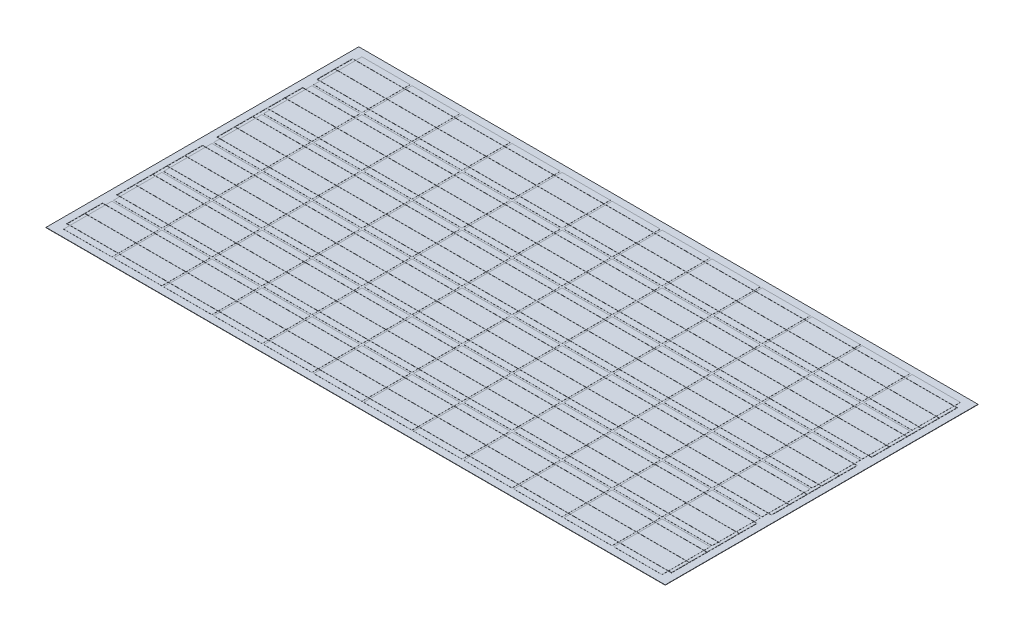
SolidWorks part; units mm, degrees
ref_plane "Front Plane" through (0, 0, 0) normal (0, 0, 1) x (1, 0, 0)
ref_plane "Top Plane" through (0, 0, 0) normal (0, 1, 0) x (1, 0, 0)
ref_plane "Right Plane" through (0, 0, 0) normal (1, 0, 0) x (0, 0, -1)
sketch "Sketch1" plane through (0, 0, 0) normal (0, 1, 0) x (1, 0, 0)
  line L0 (81.8, 76.2) -> (81.8, -76.2)
  line L1 (-76.2, 76.2) -> (76.2, 76.2)
  line L2 (-76.2, 76.2) -> (-76.2, -76.2)
  line L3 (-76.2, -76.2) -> (76.2, -76.2)
  line L4 (76.2, 76.2) -> (76.2, -76.2)
  line L5 (-76.2, 76.2) -> (76.2, -76.2) construction
  line L6 (-76.2, -76.2) -> (76.2, 76.2) construction
  line L7 (81.8, 76.2) -> (234.2, 76.2)
  line L8 (234.2, 76.2) -> (234.2, -76.2)
  line L9 (81.8, -76.2) -> (234.2, -76.2)
  line L10 (239.8, 76.2) -> (239.8, -76.2)
  line L11 (239.8, 76.2) -> (392.2, 76.2)
  line L12 (392.2, 76.2) -> (392.2, -76.2)
  line L13 (239.8, -76.2) -> (392.2, -76.2)
  line L14 (397.8, 76.2) -> (397.8, -76.2)
  line L15 (397.8, 76.2) -> (550.2, 76.2)
  line L16 (550.2, 76.2) -> (550.2, -76.2)
  line L17 (397.8, -76.2) -> (550.2, -76.2)
  line L18 (555.8, 76.2) -> (555.8, -76.2)
  line L19 (555.8, 76.2) -> (708.2, 76.2)
  line L20 (708.2, 76.2) -> (708.2, -76.2)
  line L21 (555.8, -76.2) -> (708.2, -76.2)
  line L22 (713.8, 76.2) -> (713.8, -76.2)
  line L23 (713.8, 76.2) -> (866.2, 76.2)
  line L24 (866.2, 76.2) -> (866.2, -76.2)
  line L25 (713.8, -76.2) -> (866.2, -76.2)
  line L26 (871.8, 76.2) -> (871.8, -76.2)
  line L27 (871.8, 76.2) -> (1024.2, 76.2)
  line L28 (1024.2, 76.2) -> (1024.2, -76.2)
  line L29 (871.8, -76.2) -> (1024.2, -76.2)
  line L30 (1029.8, 76.2) -> (1029.8, -76.2)
  line L31 (1029.8, 76.2) -> (1182.2, 76.2)
  line L32 (1182.2, 76.2) -> (1182.2, -76.2)
  line L33 (1029.8, -76.2) -> (1182.2, -76.2)
  line L34 (1187.8, 76.2) -> (1187.8, -76.2)
  line L35 (1187.8, 76.2) -> (1340.2, 76.2)
  line L36 (1340.2, 76.2) -> (1340.2, -76.2)
  line L37 (1187.8, -76.2) -> (1340.2, -76.2)
  line L38 (1345.8, 76.2) -> (1345.8, -76.2)
  line L39 (1345.8, 76.2) -> (1498.2, 76.2)
  line L40 (1498.2, 76.2) -> (1498.2, -76.2)
  line L41 (1345.8, -76.2) -> (1498.2, -76.2)
  line L42 (1503.8, 76.2) -> (1503.8, -76.2)
  line L43 (1503.8, 76.2) -> (1656.2, 76.2)
  line L44 (1656.2, 76.2) -> (1656.2, -76.2)
  line L45 (1503.8, -76.2) -> (1656.2, -76.2)
  line L46 (1661.8, 76.2) -> (1661.8, -76.2)
  line L47 (1661.8, 76.2) -> (1814.2, 76.2)
  line L48 (1814.2, 76.2) -> (1814.2, -76.2)
  line L49 (1661.8, -76.2) -> (1814.2, -76.2)
  line L50 (81.8, 234.2) -> (81.8, 81.8)
  line L51 (81.8, 234.2) -> (234.2, 234.2)
  line L52 (234.2, 234.2) -> (234.2, 81.8)
  line L53 (81.8, 81.8) -> (234.2, 81.8)
  line L54 (239.8, 234.2) -> (239.8, 81.8)
  line L55 (239.8, 234.2) -> (392.2, 234.2)
  line L56 (392.2, 234.2) -> (392.2, 81.8)
  line L57 (239.8, 81.8) -> (392.2, 81.8)
  line L58 (397.8, 234.2) -> (397.8, 81.8)
  line L59 (397.8, 234.2) -> (550.2, 234.2)
  line L60 (550.2, 234.2) -> (550.2, 81.8)
  line L61 (397.8, 81.8) -> (550.2, 81.8)
  line L62 (555.8, 234.2) -> (555.8, 81.8)
  line L63 (555.8, 234.2) -> (708.2, 234.2)
  line L64 (708.2, 234.2) -> (708.2, 81.8)
  line L65 (555.8, 81.8) -> (708.2, 81.8)
  line L66 (713.8, 234.2) -> (713.8, 81.8)
  line L67 (713.8, 234.2) -> (866.2, 234.2)
  line L68 (866.2, 234.2) -> (866.2, 81.8)
  line L69 (713.8, 81.8) -> (866.2, 81.8)
  line L70 (871.8, 234.2) -> (871.8, 81.8)
  line L71 (871.8, 234.2) -> (1024.2, 234.2)
  line L72 (1024.2, 234.2) -> (1024.2, 81.8)
  line L73 (871.8, 81.8) -> (1024.2, 81.8)
  line L74 (1029.8, 234.2) -> (1029.8, 81.8)
  line L75 (1029.8, 234.2) -> (1182.2, 234.2)
  line L76 (1182.2, 234.2) -> (1182.2, 81.8)
  line L77 (1029.8, 81.8) -> (1182.2, 81.8)
  line L78 (1187.8, 234.2) -> (1187.8, 81.8)
  line L79 (1187.8, 234.2) -> (1340.2, 234.2)
  line L80 (1340.2, 234.2) -> (1340.2, 81.8)
  line L81 (1187.8, 81.8) -> (1340.2, 81.8)
  line L82 (1345.8, 234.2) -> (1345.8, 81.8)
  line L83 (1345.8, 234.2) -> (1498.2, 234.2)
  line L84 (1498.2, 234.2) -> (1498.2, 81.8)
  line L85 (1345.8, 81.8) -> (1498.2, 81.8)
  line L86 (1503.8, 234.2) -> (1503.8, 81.8)
  line L87 (1503.8, 234.2) -> (1656.2, 234.2)
  line L88 (1656.2, 234.2) -> (1656.2, 81.8)
  line L89 (1503.8, 81.8) -> (1656.2, 81.8)
  line L90 (1661.8, 234.2) -> (1661.8, 81.8)
  line L91 (1661.8, 234.2) -> (1814.2, 234.2)
  line L92 (1814.2, 234.2) -> (1814.2, 81.8)
  line L93 (1661.8, 81.8) -> (1814.2, 81.8)
  line L94 (81.8, 392.2) -> (81.8, 239.8)
  line L95 (81.8, 392.2) -> (234.2, 392.2)
  line L96 (234.2, 392.2) -> (234.2, 239.8)
  line L97 (81.8, 239.8) -> (234.2, 239.8)
  line L98 (239.8, 392.2) -> (239.8, 239.8)
  line L99 (239.8, 392.2) -> (392.2, 392.2)
  line L100 (392.2, 392.2) -> (392.2, 239.8)
  line L101 (239.8, 239.8) -> (392.2, 239.8)
  line L102 (397.8, 392.2) -> (397.8, 239.8)
  line L103 (397.8, 392.2) -> (550.2, 392.2)
  line L104 (550.2, 392.2) -> (550.2, 239.8)
  line L105 (397.8, 239.8) -> (550.2, 239.8)
  line L106 (555.8, 392.2) -> (555.8, 239.8)
  line L107 (555.8, 392.2) -> (708.2, 392.2)
  line L108 (708.2, 392.2) -> (708.2, 239.8)
  line L109 (555.8, 239.8) -> (708.2, 239.8)
  line L110 (713.8, 392.2) -> (713.8, 239.8)
  line L111 (713.8, 392.2) -> (866.2, 392.2)
  line L112 (866.2, 392.2) -> (866.2, 239.8)
  line L113 (713.8, 239.8) -> (866.2, 239.8)
  line L114 (871.8, 392.2) -> (871.8, 239.8)
  line L115 (871.8, 392.2) -> (1024.2, 392.2)
  line L116 (1024.2, 392.2) -> (1024.2, 239.8)
  line L117 (871.8, 239.8) -> (1024.2, 239.8)
  line L118 (1029.8, 392.2) -> (1029.8, 239.8)
  line L119 (1029.8, 392.2) -> (1182.2, 392.2)
  line L120 (1182.2, 392.2) -> (1182.2, 239.8)
  line L121 (1029.8, 239.8) -> (1182.2, 239.8)
  line L122 (1187.8, 392.2) -> (1187.8, 239.8)
  line L123 (1187.8, 392.2) -> (1340.2, 392.2)
  line L124 (1340.2, 392.2) -> (1340.2, 239.8)
  line L125 (1187.8, 239.8) -> (1340.2, 239.8)
  line L126 (1345.8, 392.2) -> (1345.8, 239.8)
  line L127 (1345.8, 392.2) -> (1498.2, 392.2)
  line L128 (1498.2, 392.2) -> (1498.2, 239.8)
  line L129 (1345.8, 239.8) -> (1498.2, 239.8)
  line L130 (1503.8, 392.2) -> (1503.8, 239.8)
  line L131 (1503.8, 392.2) -> (1656.2, 392.2)
  line L132 (1656.2, 392.2) -> (1656.2, 239.8)
  line L133 (1503.8, 239.8) -> (1656.2, 239.8)
  line L134 (1661.8, 392.2) -> (1661.8, 239.8)
  line L135 (1661.8, 392.2) -> (1814.2, 392.2)
  line L136 (1814.2, 392.2) -> (1814.2, 239.8)
  line L137 (1661.8, 239.8) -> (1814.2, 239.8)
  line L138 (81.8, 550.2) -> (81.8, 397.8)
  line L139 (81.8, 550.2) -> (234.2, 550.2)
  line L140 (234.2, 550.2) -> (234.2, 397.8)
  line L141 (81.8, 397.8) -> (234.2, 397.8)
  line L142 (239.8, 550.2) -> (239.8, 397.8)
  line L143 (239.8, 550.2) -> (392.2, 550.2)
  line L144 (392.2, 550.2) -> (392.2, 397.8)
  line L145 (239.8, 397.8) -> (392.2, 397.8)
  line L146 (397.8, 550.2) -> (397.8, 397.8)
  line L147 (397.8, 550.2) -> (550.2, 550.2)
  line L148 (550.2, 550.2) -> (550.2, 397.8)
  line L149 (397.8, 397.8) -> (550.2, 397.8)
  line L150 (555.8, 550.2) -> (555.8, 397.8)
  line L151 (555.8, 550.2) -> (708.2, 550.2)
  line L152 (708.2, 550.2) -> (708.2, 397.8)
  line L153 (555.8, 397.8) -> (708.2, 397.8)
  line L154 (713.8, 550.2) -> (713.8, 397.8)
  line L155 (713.8, 550.2) -> (866.2, 550.2)
  line L156 (866.2, 550.2) -> (866.2, 397.8)
  line L157 (713.8, 397.8) -> (866.2, 397.8)
  line L158 (871.8, 550.2) -> (871.8, 397.8)
  line L159 (871.8, 550.2) -> (1024.2, 550.2)
  line L160 (1024.2, 550.2) -> (1024.2, 397.8)
  line L161 (871.8, 397.8) -> (1024.2, 397.8)
  line L162 (1029.8, 550.2) -> (1029.8, 397.8)
  line L163 (1029.8, 550.2) -> (1182.2, 550.2)
  line L164 (1182.2, 550.2) -> (1182.2, 397.8)
  line L165 (1029.8, 397.8) -> (1182.2, 397.8)
  line L166 (1187.8, 550.2) -> (1187.8, 397.8)
  line L167 (1187.8, 550.2) -> (1340.2, 550.2)
  line L168 (1340.2, 550.2) -> (1340.2, 397.8)
  line L169 (1187.8, 397.8) -> (1340.2, 397.8)
  line L170 (1345.8, 550.2) -> (1345.8, 397.8)
  line L171 (1345.8, 550.2) -> (1498.2, 550.2)
  line L172 (1498.2, 550.2) -> (1498.2, 397.8)
  line L173 (1345.8, 397.8) -> (1498.2, 397.8)
  line L174 (1503.8, 550.2) -> (1503.8, 397.8)
  line L175 (1503.8, 550.2) -> (1656.2, 550.2)
  line L176 (1656.2, 550.2) -> (1656.2, 397.8)
  line L177 (1503.8, 397.8) -> (1656.2, 397.8)
  line L178 (1661.8, 550.2) -> (1661.8, 397.8)
  line L179 (1661.8, 550.2) -> (1814.2, 550.2)
  line L180 (1814.2, 550.2) -> (1814.2, 397.8)
  line L181 (1661.8, 397.8) -> (1814.2, 397.8)
  line L182 (81.8, 708.2) -> (81.8, 555.8)
  line L183 (81.8, 708.2) -> (234.2, 708.2)
  line L184 (234.2, 708.2) -> (234.2, 555.8)
  line L185 (81.8, 555.8) -> (234.2, 555.8)
  line L186 (239.8, 708.2) -> (239.8, 555.8)
  line L187 (239.8, 708.2) -> (392.2, 708.2)
  line L188 (392.2, 708.2) -> (392.2, 555.8)
  line L189 (239.8, 555.8) -> (392.2, 555.8)
  line L190 (397.8, 708.2) -> (397.8, 555.8)
  line L191 (397.8, 708.2) -> (550.2, 708.2)
  line L192 (550.2, 708.2) -> (550.2, 555.8)
  line L193 (397.8, 555.8) -> (550.2, 555.8)
  line L194 (555.8, 708.2) -> (555.8, 555.8)
  line L195 (555.8, 708.2) -> (708.2, 708.2)
  line L196 (708.2, 708.2) -> (708.2, 555.8)
  line L197 (555.8, 555.8) -> (708.2, 555.8)
  line L198 (713.8, 708.2) -> (713.8, 555.8)
  line L199 (713.8, 708.2) -> (866.2, 708.2)
  line L200 (866.2, 708.2) -> (866.2, 555.8)
  line L201 (713.8, 555.8) -> (866.2, 555.8)
  line L202 (871.8, 708.2) -> (871.8, 555.8)
  line L203 (871.8, 708.2) -> (1024.2, 708.2)
  line L204 (1024.2, 708.2) -> (1024.2, 555.8)
  line L205 (871.8, 555.8) -> (1024.2, 555.8)
  line L206 (1029.8, 708.2) -> (1029.8, 555.8)
  line L207 (1029.8, 708.2) -> (1182.2, 708.2)
  line L208 (1182.2, 708.2) -> (1182.2, 555.8)
  line L209 (1029.8, 555.8) -> (1182.2, 555.8)
  line L210 (1187.8, 708.2) -> (1187.8, 555.8)
  line L211 (1187.8, 708.2) -> (1340.2, 708.2)
  line L212 (1340.2, 708.2) -> (1340.2, 555.8)
  line L213 (1187.8, 555.8) -> (1340.2, 555.8)
  line L214 (1345.8, 708.2) -> (1345.8, 555.8)
  line L215 (1345.8, 708.2) -> (1498.2, 708.2)
  line L216 (1498.2, 708.2) -> (1498.2, 555.8)
  line L217 (1345.8, 555.8) -> (1498.2, 555.8)
  line L218 (1503.8, 708.2) -> (1503.8, 555.8)
  line L219 (1503.8, 708.2) -> (1656.2, 708.2)
  line L220 (1656.2, 708.2) -> (1656.2, 555.8)
  line L221 (1503.8, 555.8) -> (1656.2, 555.8)
  line L222 (1661.8, 708.2) -> (1661.8, 555.8)
  line L223 (1661.8, 708.2) -> (1814.2, 708.2)
  line L224 (1814.2, 708.2) -> (1814.2, 555.8)
  line L225 (1661.8, 555.8) -> (1814.2, 555.8)
  line L226 (81.8, 866.2) -> (81.8, 713.8)
  line L227 (81.8, 866.2) -> (234.2, 866.2)
  line L228 (234.2, 866.2) -> (234.2, 713.8)
  line L229 (81.8, 713.8) -> (234.2, 713.8)
  line L230 (239.8, 866.2) -> (239.8, 713.8)
  line L231 (239.8, 866.2) -> (392.2, 866.2)
  line L232 (392.2, 866.2) -> (392.2, 713.8)
  line L233 (239.8, 713.8) -> (392.2, 713.8)
  line L234 (397.8, 866.2) -> (397.8, 713.8)
  line L235 (397.8, 866.2) -> (550.2, 866.2)
  line L236 (550.2, 866.2) -> (550.2, 713.8)
  line L237 (397.8, 713.8) -> (550.2, 713.8)
  line L238 (555.8, 866.2) -> (555.8, 713.8)
  line L239 (555.8, 866.2) -> (708.2, 866.2)
  line L240 (708.2, 866.2) -> (708.2, 713.8)
  line L241 (555.8, 713.8) -> (708.2, 713.8)
  line L242 (713.8, 866.2) -> (713.8, 713.8)
  line L243 (713.8, 866.2) -> (866.2, 866.2)
  line L244 (866.2, 866.2) -> (866.2, 713.8)
  line L245 (713.8, 713.8) -> (866.2, 713.8)
  line L246 (871.8, 866.2) -> (871.8, 713.8)
  line L247 (871.8, 866.2) -> (1024.2, 866.2)
  line L248 (1024.2, 866.2) -> (1024.2, 713.8)
  line L249 (871.8, 713.8) -> (1024.2, 713.8)
  line L250 (1029.8, 866.2) -> (1029.8, 713.8)
  line L251 (1029.8, 866.2) -> (1182.2, 866.2)
  line L252 (1182.2, 866.2) -> (1182.2, 713.8)
  line L253 (1029.8, 713.8) -> (1182.2, 713.8)
  line L254 (1187.8, 866.2) -> (1187.8, 713.8)
  line L255 (1187.8, 866.2) -> (1340.2, 866.2)
  line L256 (1340.2, 866.2) -> (1340.2, 713.8)
  line L257 (1187.8, 713.8) -> (1340.2, 713.8)
  line L258 (1345.8, 866.2) -> (1345.8, 713.8)
  line L259 (1345.8, 866.2) -> (1498.2, 866.2)
  line L260 (1498.2, 866.2) -> (1498.2, 713.8)
  line L261 (1345.8, 713.8) -> (1498.2, 713.8)
  line L262 (1503.8, 866.2) -> (1503.8, 713.8)
  line L263 (1503.8, 866.2) -> (1656.2, 866.2)
  line L264 (1656.2, 866.2) -> (1656.2, 713.8)
  line L265 (1503.8, 713.8) -> (1656.2, 713.8)
  line L266 (1661.8, 866.2) -> (1661.8, 713.8)
  line L267 (1661.8, 866.2) -> (1814.2, 866.2)
  line L268 (1814.2, 866.2) -> (1814.2, 713.8)
  line L269 (1661.8, 713.8) -> (1814.2, 713.8)
  line L270 (-76.2, 234.2) -> (-76.2, 81.8)
  line L271 (-76.2, 234.2) -> (76.2, 234.2)
  line L272 (76.2, 234.2) -> (76.2, 81.8)
  line L273 (-76.2, 81.8) -> (76.2, 81.8)
  line L274 (-76.2, 392.2) -> (-76.2, 239.8)
  line L275 (-76.2, 392.2) -> (76.2, 392.2)
  line L276 (76.2, 392.2) -> (76.2, 239.8)
  line L277 (-76.2, 239.8) -> (76.2, 239.8)
  line L278 (-76.2, 550.2) -> (-76.2, 397.8)
  line L279 (-76.2, 550.2) -> (76.2, 550.2)
  line L280 (76.2, 550.2) -> (76.2, 397.8)
  line L281 (-76.2, 397.8) -> (76.2, 397.8)
  line L282 (-76.2, 708.2) -> (-76.2, 555.8)
  line L283 (-76.2, 708.2) -> (76.2, 708.2)
  line L284 (76.2, 708.2) -> (76.2, 555.8)
  line L285 (-76.2, 555.8) -> (76.2, 555.8)
  line L286 (-76.2, 866.2) -> (-76.2, 713.8)
  line L287 (-76.2, 866.2) -> (76.2, 866.2)
  line L288 (76.2, 866.2) -> (76.2, 713.8)
  line L289 (-76.2, 713.8) -> (76.2, 713.8)
  line L290 (-76.2, 76.2) -> (81.8, 76.2) construction
  line L291 (-76.2, 76.2) -> (-76.2, 234.2) construction
  point P0 (0, 0)
  dimension "D1" = 152.4
  dimension "D2" = 152.4
  dimension "D5" = 158
  dimension "D6" = 158
  dimension "D3" = 12
  dimension "D4" = 6
extrude "Boss-Extrude1" add sketch "Sketch1" along normal blind 0.3
sketch "Sketch2" plane through (0, 0, 0) normal (0, -1, 0) x (1, 0, 0)
  line L1 (1846.9962, -889) -> (-109.0038, -889)
  line L2 (1846.9962, -889) -> (1846.9962, 99)
  line L3 (1846.9962, 99) -> (-109.0038, 99)
  line L4 (-109.0038, -889) -> (-109.0038, 99)
  line L5 (1846.9962, -889) -> (-109.0038, 99) construction
  line L6 (1846.9962, 99) -> (-109.0038, -889) construction
  line L9 (866.2, -397.8) -> (866.2, -550.2) construction
  line L10 (1024.2, -392.2) -> (871.8, -392.2) construction
  point P0 (868.9962, -395)
  point P5 (0, 0)
  point P6 (868.9618, -395.0845)
  point P7 (868.8142, -395.0837)
  point P8 (0, 0)
  point P10 (0, 0)
  point P11 (868.9962, -394.7196)
  dimension "D1" = 1956
  dimension "D2" = 988
  dimension "D3" = 2.7962
  dimension "D4" = 2.8
extrude "Boss-Extrude2" add sketch "Sketch2" along normal blind 1
sketch "Sketch5" plane through (0, -1, 0) normal (0, -1, 0) x (1, 0, 0)
  line L0 (-109.0038, 99) -> (-109.0038, -889) construction
  line L1 (125.9962, -305) -> (40.9962, -305)
  line L2 (125.9962, -305) -> (125.9962, -485)
  line L3 (125.9962, -485) -> (40.9962, -485)
  line L4 (40.9962, -305) -> (40.9962, -485)
  line L5 (125.9962, -305) -> (40.9962, -485) construction
  line L6 (125.9962, -485) -> (40.9962, -305) construction
  point P0 (83.4962, -395)
  point P7 (40.9962, -395)
  point P8 (-109.0038, -395)
  dimension "D1" = 180
  dimension "D2" = 85
  dimension "D3" = 150
extrude "Boss-Extrude3" add sketch "Sketch5" along normal blind 20
sketch "Sketch3" plane through (0, 0.3, 0) normal (0, 1, 0) x (1, 0, 0)
  line L0 (1824.2, 846.2) -> (1824.2, 575.8)
  line L1 (1824.2, 530.2) -> (1824.2, 259.8)
  line L2 (1824.2, -56.2) -> (1824.2, 214.2)
  line L3 (1814.2, 81.8) -> (1814.2, 234.2) construction
  line L4 (1814.2, 866.2) -> (1661.8, 866.2) construction
  line L5 (-86.2, 417.8) -> (-86.2, 688.2)
  line L6 (-86.2, 372.2) -> (-86.2, 101.8)
  line L7 (-86.2, 846.2) -> (-86.2, 733.8)
  line L8 (-86.2, -56.2) -> (-86.2, 56.2)
  line L9 (-76.2, 866.2) -> (-76.2, 713.8) construction
  line L11 (-86.2, 846.2) -> (1824.2, 846.2)
  line L12 (-86.2, 733.8) -> (1824.2, 733.8)
  line L13 (-86.2, 790) -> (1824.2, 790)
  line L14 (1824.2, 688.2) -> (-86.2, 688.2)
  line L15 (-86.2, 575.8) -> (1824.2, 575.8)
  line L16 (-86.2, 530.2) -> (1824.2, 530.2)
  line L17 (-86.2, 259.8) -> (1824.2, 259.8)
  line L18 (-86.2, 214.2) -> (1824.2, 214.2)
  line L19 (1824.2, 101.8) -> (-86.2, 101.8)
  line L20 (1824.2, 56.2) -> (-86.2, 56.2)
  line L21 (1824.2, -56.2) -> (-86.2, -56.2)
  line L22 (-86.2, 0) -> (1824.2, 0)
  line L23 (1824.2, 372.2) -> (-86.2, 372.2)
  line L24 (1824.2, 417.8) -> (-86.2, 417.8)
  line L25 (-86.2, 632) -> (1824.2, 632)
  line L26 (-86.2, 474) -> (1824.2, 474)
  line L27 (-86.2, 316) -> (1824.2, 316)
  line L28 (-86.2, 158) -> (1824.2, 158)
  point P45 (1824.2, 0)
  dimension "D1" = 10
  dimension "D2" = 20
  dimension "D3" = 20
  dimension "D4" = 20
  dimension "D5" = 20
  dimension "D6" = 20
  dimension "D7" = 20
  dimension "D8" = 10
  dimension "D9" = 20
  dimension "D10" = 20
  dimension "D11" = 20
  dimension "D12" = 20
  dimension "D13" = 20
  dimension "D14" = 20
  dimension "D15" = 20
  dimension "D16" = 20
  dimension "D17" = 56.2
  dimension "D18" = 56.2
  dimension "D19" = 56.2
  dimension "D20" = 56.2
sketch "Sketch6" plane through (-76.2, 0, 0) normal (-1, 0, 0) x (0, 0, 1)
  line L0 (56.2, 0.3) -> (-214.2, 0.3) construction
  line L1 (-76.2, 0.3) -> (76.2, 0.3) construction
  circle A0 centre (56.2, 0.3) radius 0.25
  circle A1 centre (0, 0.3) radius 0.25
  circle A2 centre (-56.2, 0.3) radius 0.25
  circle A3 centre (-101.8, 0.3) radius 0.25
  circle A4 centre (-214.2, 0.3) radius 0.25
  circle A5 centre (-259.8, 0.3) radius 0.25
  circle A6 centre (-316, 0.3) radius 0.25
  circle A7 centre (-158, 0.3) radius 0.25
  circle A8 centre (-530.2, 0.3) radius 0.25
  circle A9 centre (-372.2, 0.3) radius 0.25
  circle A10 centre (-417.8, 0.3) radius 0.25
  circle A11 centre (-474, 0.3) radius 0.25
  circle A12 centre (-575.8, 0.3) radius 0.25
  circle A13 centre (-632, 0.3) radius 0.25
  circle A14 centre (-688.2, 0.3) radius 0.25
  circle A15 centre (-733.8, 0.3) radius 0.25
  circle A16 centre (-790, 0.3) radius 0.25
  circle A17 centre (-846.2, 0.3) radius 0.25
  point P9 (53.7397, 0.25)
  point P10 (41.8649, 0.7283)
  point P11 (33.0873, 1.1537)
  point P12 (24.6039, 0.9554)
  point P13 (1.1105, 1.1057)
  point P17 (-0.6534, 0.1894)
  point P23 (-0.2527, -0.1322)
  point P24 (0, 0)
  point P30 (-101.8, 0.3)
  point P33 (0, 0)
  point P35 (0, 0)
  point P37 (0, 0)
  point P39 (0, 0)
  point P49 (0, 0)
  point P51 (0, 0)
  point P53 (0, 0)
  point P55 (0, 0)
  point P69 (0, 0)
  point P71 (0, 0)
  point P73 (0, 0)
  point P75 (0, 0)
  point P77 (0, 0)
  point P79 (0, 0)
  dimension "D1" = 0.5
  dimension "D2" = 0.5
  dimension "D3" = 0.5
  dimension "D4" = 0.5
  dimension "D5" = 0.5
  dimension "D6" = 0.5
  dimension "D7" = 0.5
  dimension "D8" = 0.5
  dimension "D9" = 0.5
  dimension "D10" = 0.5
  dimension "D11" = 0.5
  dimension "D12" = 0.5
  dimension "D13" = 0.5
  dimension "D14" = 0.5
  dimension "D15" = 0.5
  dimension "D16" = 0.5
  dimension "D17" = 0.5
  dimension "D18" = 0.5
sweep "Sweep3" add profiles "Sketch6" path "Sketch3"
sketch "Sketch7" plane through (0, 0, 0) normal (0, 1, 0) x (1, 0, 0)
  line L0 (-76.2, 56.45) -> (-86.2, 56.45) construction
  line L1 (-85.2, 56.45) -> (-86.2, 56.45)
  line L2 (-85.2, 56.45) -> (-85.2, -56.45)
  line L3 (-85.2, -56.45) -> (-86.2, -56.45)
  line L4 (-86.2, 56.45) -> (-86.2, -56.45)
  line L5 (-76.2, 372.45) -> (-86.2, 372.45) construction
  line L6 (-86.2, 101.55) -> (-85.2, 101.55)
  line L7 (-86.2, 101.55) -> (-86.2, 372.45)
  line L8 (-86.2, 372.45) -> (-85.2, 372.45)
  line L9 (-85.2, 101.55) -> (-85.2, 372.45)
  line L10 (-86.2, 417.55) -> (-76.2, 417.55) construction
  line L11 (-86.2, 688.45) -> (-85.2, 688.45)
  line L12 (-86.2, 688.45) -> (-86.2, 417.55)
  line L13 (-86.2, 417.55) -> (-85.2, 417.55)
  line L14 (-85.2, 688.45) -> (-85.2, 417.55)
  line L15 (-86.2, 733.55) -> (-76.2, 733.55) construction
  line L16 (-86.2, 846.45) -> (-85.2, 846.45)
  line L17 (-86.2, 846.45) -> (-86.2, 733.55)
  line L18 (-86.2, 733.55) -> (-85.2, 733.55)
  line L19 (-85.2, 846.45) -> (-85.2, 733.55)
  line L20 (-86.2, -55.95) -> (-86.2, -56.45) construction
  line L21 (1814.2, 575.55) -> (1824.2, 575.55) construction
  line L22 (1824.2, 846.45) -> (1823.2, 846.45)
  line L23 (1824.2, 846.45) -> (1824.2, 575.55)
  line L24 (1824.2, 575.55) -> (1823.2, 575.55)
  line L25 (1823.2, 846.45) -> (1823.2, 575.55)
  line L26 (1814.2, 259.55) -> (1824.2, 259.55) construction
  line L27 (1824.2, 530.45) -> (1823.2, 530.45)
  line L28 (1824.2, 530.45) -> (1824.2, 259.55)
  line L29 (1824.2, 259.55) -> (1823.2, 259.55)
  line L30 (1823.2, 530.45) -> (1823.2, 259.55)
  line L31 (1814.2, -56.45) -> (1824.2, -56.45) construction
  line L32 (1824.2, 214.45) -> (1823.2, 214.45)
  line L33 (1824.2, 214.45) -> (1824.2, -56.45)
  line L34 (1824.2, -56.45) -> (1823.2, -56.45)
  line L35 (1823.2, 214.45) -> (1823.2, -56.45)
  dimension "D1" = 1
  dimension "D2" = 1
extrude "Boss-Extrude4" add sketch "Sketch7" along normal blind 0.5
